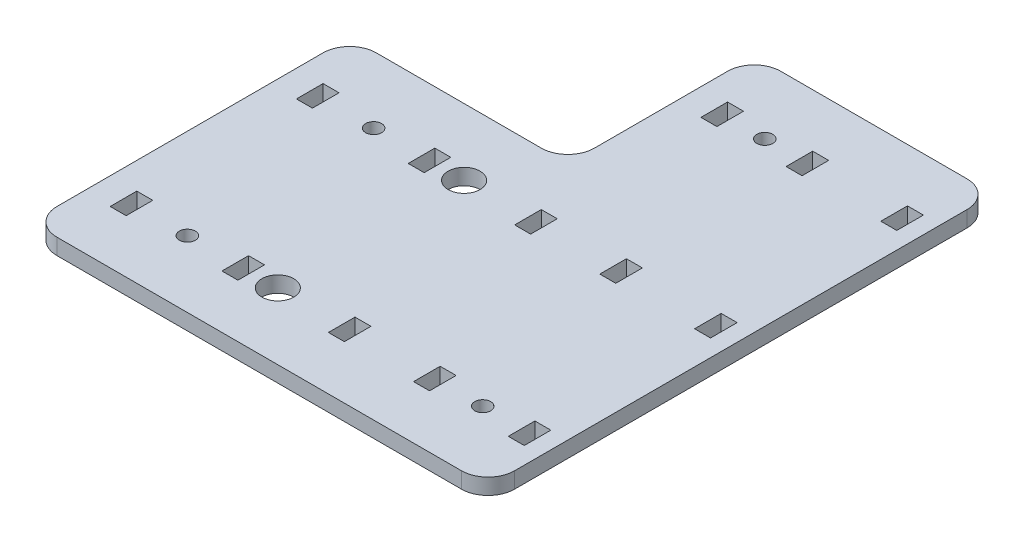
SolidWorks part; units mm, degrees
ref_plane "Front Plane" through (0, 0, 0) normal (0, 0, 1) x (1, 0, 0)
ref_plane "Top Plane" through (0, 0, 0) normal (0, 1, 0) x (1, 0, 0)
ref_plane "Right Plane" through (0, 0, 0) normal (1, 0, 0) x (0, 0, -1)
sketch "Sketch1" plane through (0, 0, 0) normal (0, 1, 0) x (1, 0, 0)
  line L1 (0, 0) -> (86, 0)
  line L2 (0, 0) -> (0, 60)
  line L3 (0, 60) -> (86, 60)
  line L4 (86, 0) -> (86, 60)
  dimension "D1" = 60
  dimension "D2" = 86
extrude "Boss-Extrude1" add sketch "Sketch1" along normal blind 3
ref_plane "Plane6" through (0, 0, -55) normal (0, 0, -1) x (-1, 0, 0)
ref_plane "Plane1" through (0, 0, -30) normal (0, 0, 1) x (1, 0, 0)
sketch "Sketch4" plane through (0, 0, -60) normal (0, 0, -1) x (-1, 0, 0)
  line L0 (-86, 3) -> (0, 3) construction
  line L1 (-86, 3) -> (-41, 3)
  line L2 (-86, 3) -> (-86, 0)
  line L3 (-86, 0) -> (-41, 0)
  line L4 (-41, 3) -> (-41, 0)
  line L5 (-86, 0) -> (0, 0) construction
  dimension "D1" = 45
extrude "Boss-Extrude2" add sketch "Sketch4" along normal blind 35
sketch "Sketch2" plane through (0, 3, 0) normal (0, 1, 0) x (1, 0, 0)
  line L1 (65, 10) -> (62, 10)
  line L2 (65, 10) -> (65, 15)
  line L3 (65, 15) -> (62, 15)
  line L4 (62, 10) -> (62, 15)
  line L9 (49, 10) -> (46, 10)
  line L10 (49, 10) -> (49, 15)
  line L11 (49, 15) -> (46, 15)
  line L12 (46, 10) -> (46, 15)
  line L21 (0, 0) -> (86, 0) construction
  line L23 (79.8, 15) -> (82.8, 15)
  line L24 (79.8, 15) -> (79.8, 10)
  line L25 (79.8, 10) -> (82.8, 10)
  line L26 (82.8, 15) -> (82.8, 10)
  dimension "D1" = 3
  dimension "D2" = 13
  dimension "D3" = 3
  dimension "D6" = 3
  dimension "D7" = 14.8
  dimension "D11" = 10
  dimension "D12" = 5
extrude "Cut-Extrude1" cut sketch "Sketch2" against normal blind 3
sketch "Sketch8" plane through (0, 3, 0) normal (0, 1, 0) x (1, 0, 0)
  line L0 (49, 15) -> (46, 15) construction
  line L1 (8, 15) -> (5, 15)
  line L2 (8, 15) -> (8, 10)
  line L3 (8, 10) -> (5, 10)
  line L4 (5, 15) -> (5, 10)
  line L5 (29, 15) -> (26, 15)
  line L6 (29, 15) -> (29, 10)
  line L7 (29, 10) -> (26, 10)
  line L8 (26, 15) -> (26, 10)
  line L9 (46, 10) -> (49, 10) construction
  line L10 (46, 15) -> (46, 10) construction
  dimension "D1" = 3
  dimension "D2" = 18
  dimension "D3" = 3
  dimension "D4" = 17
extrude "Cut-Extrude10" cut sketch "Sketch8" against normal through all
pattern_linear "LPattern3" count 2 spacing 35 along (0, 0, -1) of "Cut-Extrude10"
fillet "Fillet1" radius 5 6 edges at (86, 1.5, 0) (0, 1.5, -60) (0, 1.5, 0) (86, 1.5, -95) (41, 1.5, -95) (41, 1.5, -60)
pattern_linear "LPattern1" count 3 spacing 35 along (0, 0, -1) of "Cut-Extrude1"
sketch "Sketch5" plane through (0, 3, 0) normal (0, 1, 0) x (1, 0, 0)
  line L0 (49, 85) -> (46, 85) construction
  line L1 (65, 15) -> (62, 15) construction
  line L3 (49, 80) -> (49, 85) construction
  line L4 (65, 10) -> (65, 15) construction
  line L6 (8, 45) -> (8, 50) construction
  line L7 (8, 50) -> (5, 50) construction
  circle A0 centre (17, 12.5) radius 1.5
  circle A1 centre (17, 47.5) radius 1.5
  circle A2 centre (72.5, 12.5) radius 1.5
  circle A3 centre (55.5, 82.5) radius 1.5
  dimension "D1" = 3
  dimension "D2" = 3
  dimension "D3" = 3
  dimension "D4" = 3
  dimension "D5" = 2.5
  dimension "D6" = 2.5
  dimension "D7" = 2.5
  dimension "D8" = 6.5
  dimension "D9" = 7.5
  dimension "D10" = 9
extrude "Cut-Extrude2" cut sketch "Sketch5" against normal through all
sketch "Sketch6" plane through (0, 3, 0) normal (0, 1, 0) x (1, 0, 0)
  line L0 (62, 50) -> (62, 45) construction
  line L1 (26, 45) -> (29, 45) construction
  circle A0 centre (34, 12.5) radius 3
  circle A1 centre (34, 47.5) radius 3
  dimension "D3" = 6
  dimension "D4" = 6
  dimension "D1" = 28
  dimension "D2" = 35
  dimension "D5" = 2.5
extrude "Cut-Extrude3" cut sketch "Sketch6" against normal through all
